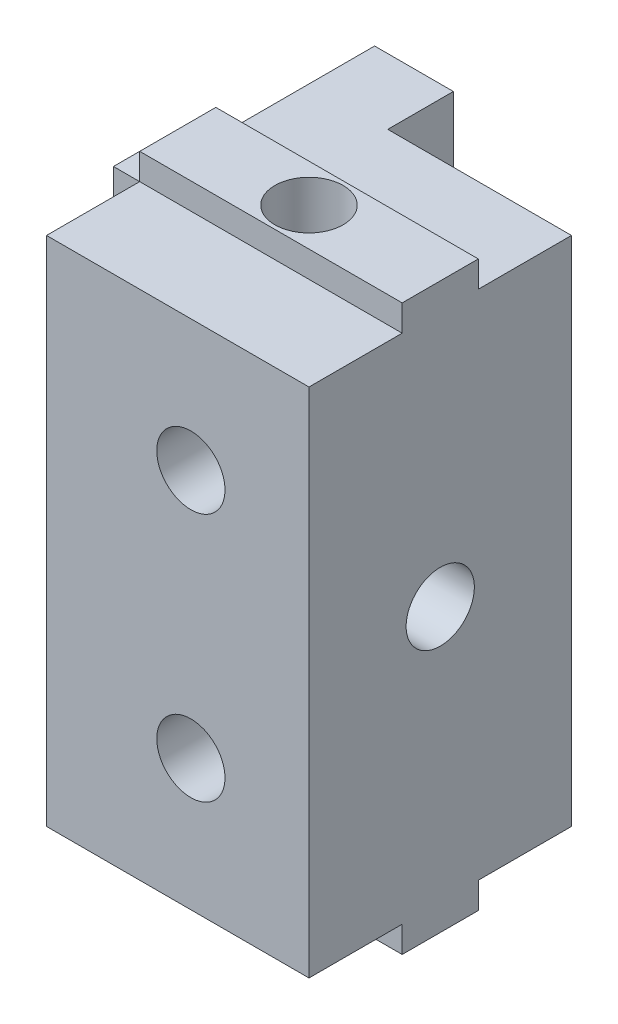
SolidWorks part; units mm, degrees
ref_plane "Front Plane" through (0, 0, 0) normal (0, 0, 1) x (1, 0, 0)
ref_plane "Top Plane" through (0, 0, 0) normal (0, 1, 0) x (1, 0, 0)
ref_plane "Right Plane" through (0, 0, 0) normal (1, 0, 0) x (0, 0, -1)
sketch "Esquisse1" plane through (0, 0, 0) normal (0, 0, 1) x (1, 0, 0)
  line L1 (-5, 9.75) -> (5, 9.75)
  line L2 (-5, 9.75) -> (-5, -9.75)
  line L3 (-5, -9.75) -> (5, -9.75)
  line L4 (5, 9.75) -> (5, -9.75)
  point P4 (5, 0)
  point P5 (0, -9.75)
  dimension "D1" = 10
  dimension "D2" = 19.5
extrude "Main" add sketch "Esquisse1" along normal mid plane 10
sketch "Sketch2" plane through (0, 0, 0) normal (0, 1, 0) x (1, 0, 0)
  line L0 (-5, -5) -> (-5, 5) construction
  line L1 (-5, -1.45) -> (5, -1.45)
  line L2 (-5, -1.45) -> (-5, 1.45)
  line L3 (-5, 1.45) -> (5, 1.45)
  line L4 (5, -1.45) -> (5, 1.45)
  line L5 (5, -5) -> (5, 5) construction
  line L6 (5, -5) -> (-5, -5) construction
  dimension "D1" = 2.9
  dimension "D2" = 3.55
extrude "MakerBeamSideSupport" add sketch "Sketch2" along normal mid plane 21.5
sketch "Sketch3" plane through (-5, 0, 0) normal (-1, 0, 0) x (0, 0, 1)
  line L1 (1.45, -9.75) -> (-1.45, -9.75)
  line L2 (1.45, -9.75) -> (1.45, 9.75)
  line L3 (1.45, 9.75) -> (-1.45, 9.75)
  line L4 (-1.45, -9.75) -> (-1.45, 9.75)
extrude "MakerBeamTopSupport" add sketch "Sketch3" along normal blind 1
sketch "Esquisse2" plane through (0, 0, -5) normal (0, 0, -1) x (-1, 0, 0)
  line L0 (-5, 9.75) -> (5, 9.75) construction
  line L1 (5, -9.75) -> (-5, -9.75) construction
  line L2 (-5, -9.75) -> (-5, 9.75) construction
  circle A0 centre (-0.5, 4.75) radius 1.3
  circle A1 centre (-0.5, -4.75) radius 1.3
  dimension "D3" = 2.6
  dimension "D1" = 5
  dimension "D2" = 5
  dimension "D4" = 4.5
  dimension "D5" = 9.5
extrude "ServoFixingHoles" cut sketch "Esquisse2" against normal blind 10
sketch "Esquisse3" plane through (-5, 0, 0) normal (-1, 0, 0) x (0, 0, 1)
  line L0 (5, 9.75) -> (5, -9.75) construction
  circle A0 centre (0, 0) radius 1.3
  dimension "D1" = 2.6
  dimension "D2" = 5
extrude "SideHoles" cut sketch "Esquisse3" against normal through all both and the other way through all
sketch "Esquisse4" plane through (0, -9.75, 0) normal (0, -1, 0) x (1, 0, 0)
  line L0 (-5, 5) -> (5, 5) construction
  circle A0 centre (0, 0) radius 1.3
  dimension "D1" = 2.6
  dimension "D2" = 5
extrude "TopHoles" cut sketch "Esquisse4" against normal through all
sketch "Sketch1" plane through (0, 0, -5) normal (0, 0, -1) x (-1, 0, 0)
  line L0 (-5, 9.75) -> (5, 9.75) construction
  line L1 (2, 9.75) -> (5, 9.75)
  line L2 (2, 9.75) -> (2, -9.75)
  line L3 (2, -9.75) -> (5, -9.75)
  line L4 (5, 9.75) -> (5, -9.75)
  dimension "D1" = 3
extrude "Boss-Extrude1" add sketch "Sketch1" along normal blind 2.5
